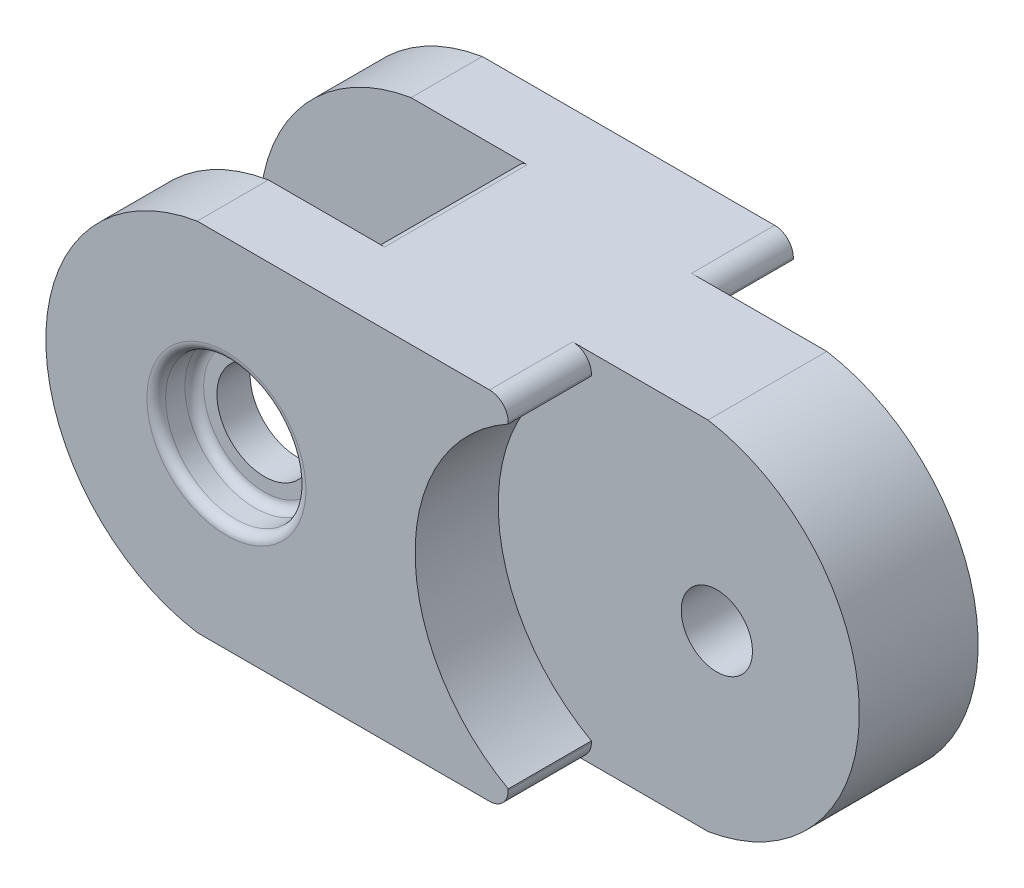
SolidWorks part; units mm, degrees
material "ABS PC"
ref_plane "Front Plane" through (0, 0, 0) normal (0, 0, 1) x (1, 0, 0)
ref_plane "Top Plane" through (0, 0, 0) normal (0, 1, 0) x (1, 0, 0)
ref_plane "Right Plane" through (0, 0, 0) normal (1, 0, 0) x (0, 0, -1)
sketch "Sketch1" plane through (0, 0, 0) normal (0, 1, 0) x (1, 0, 0)
  line L1 (-11.43, -7.62) -> (11.43, -7.62)
  line L2 (-11.43, -7.62) -> (-11.43, 7.62)
  line L3 (-11.43, 7.62) -> (11.43, 7.62)
  line L4 (11.43, -7.62) -> (11.43, 7.62)
  line L5 (-11.43, -7.62) -> (11.43, 7.62) construction
  line L6 (-11.43, 7.62) -> (11.43, -7.62) construction
  point P0 (0, 0)
  dimension "D1" = 22.86
  dimension "D2" = 15.24
extrude "Boss-Extrude1" add sketch "Sketch1" along normal blind 19.05 contours L3 L4 L1 L2
ref_plane "Plane1" through (0, 0, 7.62) normal (0, 0, 1) x (1, 0, 0)
sketch "Sketch3" plane through (0, 0, 7.62) normal (0, 0, 1) x (1, 0, 0)
  line L0 (8.382, 0) -> (-8.382, 0) construction
  line L1 (-11.43, 19.05) -> (-11.43, 0) construction
  line L2 (-11.43, 19.05) -> (-11.43, 0)
  arc A0 (-11.43, 19.05) -> (-11.43, 0) centre (-9.8694, 9.525) ccw
  dimension "D1" = 9.652
extrude "Boss-Extrude3" add sketch "Sketch3" against normal blind 3.81
pattern_linear "LPattern1" count 2 spacing 11.43 along (0, 0, -1) of "Boss-Extrude3"
sketch "Sketch5" plane through (0, 0, 7.62) normal (0, 0, 1) x (1, 0, 0)
  circle A1 centre (-9.8694, 9.525) radius 1.905
  arc A2 (-11.43, 19.05) -> (-11.43, 0) centre (-9.8694, 9.525) ccw construction
  point P3 (-19.5214, 9.525)
  dimension "D1" = 3.81
extrude "Cut-Extrude2" cut sketch "Sketch5" against normal through all
sketch "Sketch6" plane through (0, 0, 0) normal (0, 0, 1) x (1, 0, 0)
  line L0 (-11.43, 19.05) -> (-11.43, 0)
  arc A0 (-11.43, 19.05) -> (-11.43, 0) centre (-9.8694, 9.525) cw
  dimension "D1" = 9.652
extrude "Cut-Extrude3" cut sketch "Sketch6" against normal mid plane 7.62
sketch "Sketch8" plane through (0, 0, 0) normal (0, 0, 1) x (1, 0, 0)
  line L0 (11.43, 19.05) -> (11.43, 0)
  arc A0 (11.43, 19.05) -> (11.43, 0) centre (9.8694, 9.525) cw
  dimension "D1" = 9.652
extrude "Boss-Extrude6" add sketch "Sketch8" along normal mid plane 6.35
sketch "Sketch9" plane through (0, 0, 3.175) normal (0, 0, 1) x (1, 0, 0)
  circle A0 centre (11.9014, 9.525) radius 1.905
  arc A2 (11.43, 0) -> (11.43, 19.05) centre (9.8694, 9.525) ccw construction
  point P6 (19.5214, 9.525)
  dimension "D2" = 3.81
  dimension "D1" = 7.62
extrude "Cut-Extrude4" cut sketch "Sketch9" against normal blind 6.35
sketch "Sketch10" plane through (0, 0, 3.175) normal (0, 0, 1) x (1, 0, 0)
  line L0 (11.43, 19.05) -> (11.43, 0)
  arc A0 (11.43, 19.05) -> (11.43, 0) centre (9.8694, 9.525) ccw
  dimension "D1" = 9.652
extrude "Cut-Extrude5" cut sketch "Sketch10" along normal blind 4.445
pattern_linear "LPattern2" count 2 spacing 10.795 along (0, 0, -1) of "Cut-Extrude5"
hole_wizard "CBORE for #6 Pan Head Machine Screw3" positions "Sketch16" profile "Sketch15" counterbore size "#6" standard "ANSI Inch" end condition through all
sketch "Sketch16" plane through (0, 0, 7.62) normal (0, 0, 1) x (1, 0, 0)
  point P0 (-9.8694, 9.525)
sketch "Sketch15" plane through (-9.8694, 9.525, 7.62) normal (1, 0, 0) x (0, -1, 0)
  line L0 (0, 0) -> (0, 15.24)
  line L1 (0, 15.24) -> (1.875, 15.24)
  line L3 (1.875, 15.24) -> (1.875, 2.032)
  line L4 (1.875, 2.032) -> (3.75, 2.032)
  line L5 (3.75, 2.032) -> (3.75, 0)
  line L7 (3.75, 0) -> (0, 0)
  line L11 (0, -6.35) -> (0, 107.95) construction
  dimension "Thru Hole Dia." = 3.75
  dimension "Thru Hole Depth" = 15.24
  dimension "C'Bore Dia." = 7.5
  dimension "C'Bore Depth" = 2.032
sketch "Sketch18" plane through (0, 0, 5.588) normal (0, 0, 1) x (1, 0, 0)
  circle A0 centre (-9.8694, 9.525) radius 2.54
  circle A1 centre (-9.8694, 9.525) radius 1.905 construction
  dimension "D1" = 5.08
extrude "Cut-Extrude8" cut sketch "Sketch18" against normal up to surface (1.778 mm away) contours A0 up to face at (-9.8694, 9.525, 3.81)
fillet "Fillet2" radius 0.5 2 edges at (-8.3088, 0, 0) (-8.3088, 19.05, 0)
fillet "Fillet3" radius 0.5 2 edges at (-6.1194, 9.525, 5.588) (-6.1194, 9.525, 7.62)
sketch "Sketch19" plane through (0, 19.05, 0) normal (0, 1, 0) x (1, 0, 0)
  line L0 (8.3088, -3.175) -> (8.3088, -7.62)
  line L1 (8.3088, -7.62) -> (5.197, -7.62)
  line L2 (-11.43, -7.62) -> (8.3088, -7.62) construction
  line L3 (5.197, -7.62) -> (5.197, -3.175)
  line L4 (5.197, -3.175) -> (8.3088, -3.175)
  dimension "D1" = 5.197
extrude "Cut-Extrude9" cut sketch "Sketch19" against normal up to surface (19.05 mm away) up to face at (-0.0055, 0, 0)
pattern_linear "LPattern3" count 2 spacing 10.795 along (0, 0, -1) of "Cut-Extrude9"
fillet "Fillet4" radius 1 4 edges at (5.197, 0, -5.3975) (5.197, 19.05, -5.3975) (5.197, 0, 5.3975) (5.197, 19.05, 5.3975)
